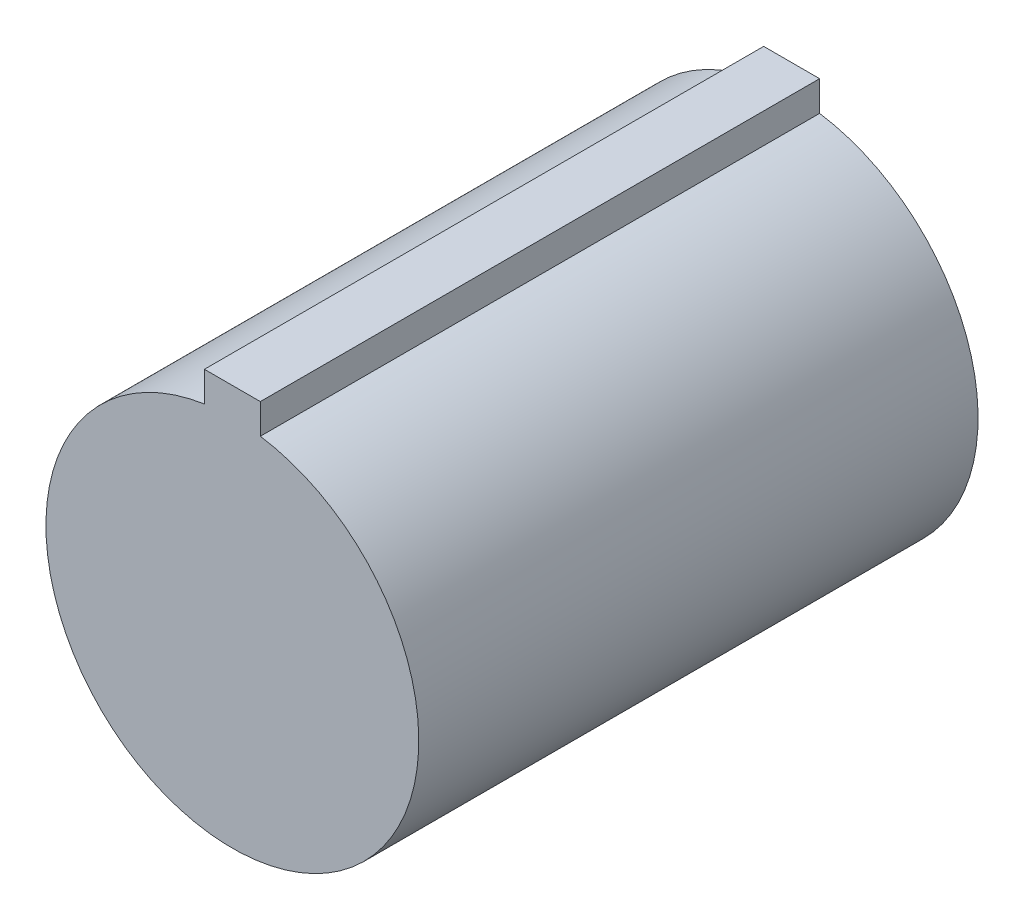
SolidWorks part; units mm, degrees
ref_plane "Front Plane" through (0, 0, 0) normal (0, 0, 1) x (1, 0, 0)
ref_plane "Top Plane" through (0, 0, 0) normal (0, 1, 0) x (1, 0, 0)
ref_plane "Right Plane" through (0, 0, 0) normal (1, 0, 0) x (0, 0, -1)
sketch "Sketch1" plane through (0, 0, 0) normal (0, 0, 1) x (1, 0, 0)
  circle A0 centre (0, 0) radius 50.8
extrude "Boss-Extrude1" add sketch "Sketch1" along normal mid plane 152.4
sketch "Sketch2" plane through (0, 0, 76.2) normal (0, 0, 1) x (1, 0, 0)
  line L2 (7.62, 50.2252) -> (7.62, 58.42)
  line L3 (7.62, 58.42) -> (-7.62, 58.42)
  line L4 (-7.62, 50.2252) -> (-7.62, 58.42)
  line L5 (0, 50.8) -> (-7.62, 58.42) construction
  line L6 (7.62, 58.42) -> (0, 50.8) construction
  circle A0 centre (0, 0) radius 50.8 construction
  arc A1 (7.62, 50.2252) -> (-7.62, 50.2252) centre (0, 0) ccw
  point P3 (0, 50.8)
  dimension "D1" = 15.24
extrude "Boss-Extrude2" add sketch "Sketch2" against normal through all
